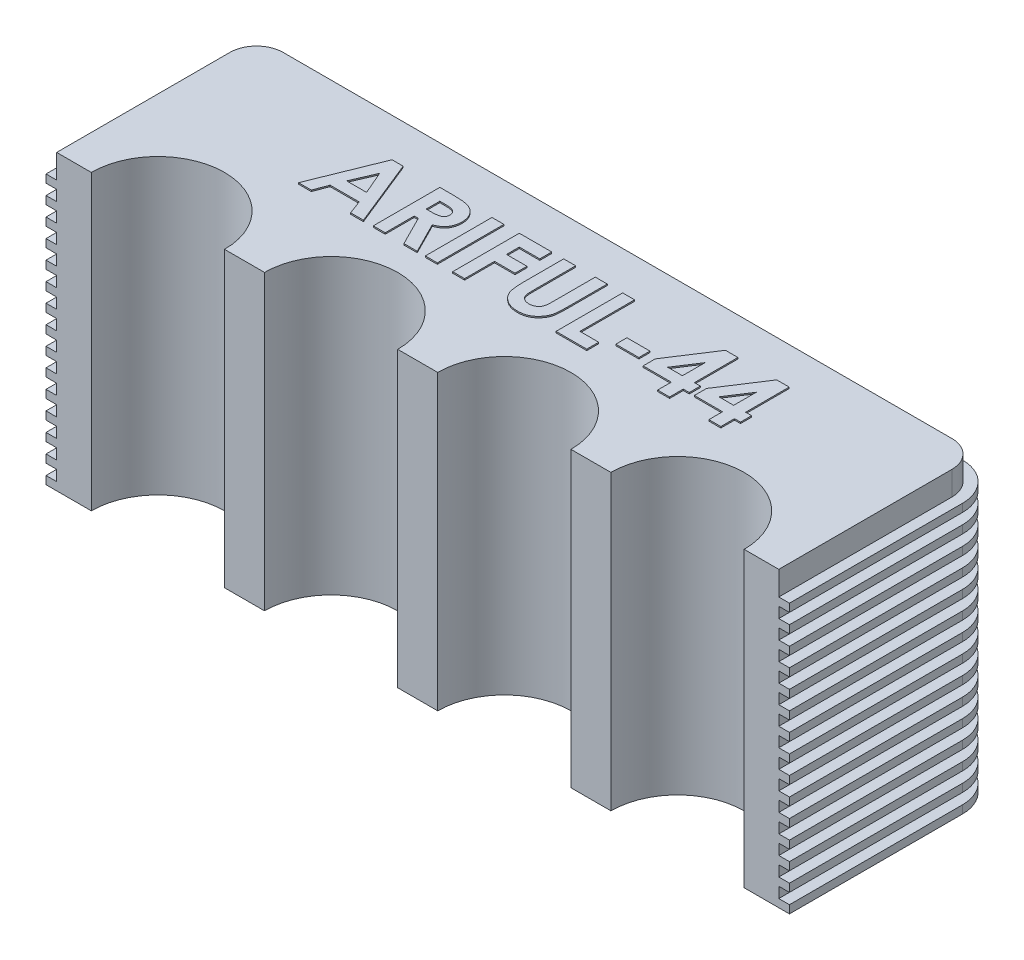
SolidWorks part; units mm, degrees
ref_plane "Front Plane" through (0, 0, 0) normal (0, 0, 1) x (1, 0, 0)
ref_plane "Top Plane" through (0, 0, 0) normal (0, 1, 0) x (1, 0, 0)
ref_plane "Right Plane" through (0, 0, 0) normal (1, 0, 0) x (0, 0, -1)
sketch "Sketch1" plane through (0, 0, 0) normal (0, 1, 0) x (1, 0, 0)
  line L0 (122.5, -37.5) -> (135.5, -37.5)
  line L1 (-135.5, -37.5) -> (-122.5, -37.5)
  line L2 (-135.5, -37.5) -> (-135.5, 27.5)
  line L3 (-125.5, 37.5) -> (125.5, 37.5)
  line L4 (135.5, -37.5) -> (135.5, 27.5)
  line L5 (-135.5, -37.5) -> (135.5, 37.5) construction
  line L6 (-135.5, 37.5) -> (135.5, -37.5) construction
  line L7 (0, 37.5) -> (0, -37.5) construction
  line L8 (57.5, -37.5) -> (72.5, -37.5)
  line L9 (-72.5, -37.5) -> (-57.5, -37.5)
  line L10 (-7.5, -37.5) -> (7.5, -37.5)
  arc A0 (125.5, 37.5) -> (135.5, 27.5) centre (125.5, 27.5) cw
  arc A1 (-135.5, 27.5) -> (-125.5, 37.5) centre (-125.5, 27.5) cw
  arc A2 (122.5, -37.5) -> (72.5, -37.5) centre (97.5, -37.5) ccw
  arc A3 (57.5, -37.5) -> (7.5, -37.5) centre (32.5, -37.5) ccw
  arc A4 (-122.5, -37.5) -> (-72.5, -37.5) centre (-97.5, -37.5) cw
  arc A5 (-57.5, -37.5) -> (-7.5, -37.5) centre (-32.5, -37.5) cw
  point P0 (0, 0)
  dimension "D1" = 10
  dimension "D4" = 25
  dimension "D6" = 50
  dimension "D2" = 271
  dimension "D3" = 65
  dimension "D5" = 13
  dimension "D7" = 15
extrude "Boss-Extrude1" add sketch "Sketch1" along normal blind 110
sketch "Sketch4" plane through (0, 0, 0) normal (0, 1, 0) x (1, 0, 0)
  line L8 (-135.5, -37.5) -> (-139.5, -37.5)
  line L9 (135.5, -37.5) -> (139.5, -37.5)
  line L16 (-139.5, 27.5) -> (-139.5, -41.5)
  line L17 (125.5, 41.5) -> (-125.5, 41.5)
  line L18 (139.5, -41.5) -> (139.5, 27.5)
  line L19 (118.1155, -41.5) -> (139.5, -41.5)
  line L20 (53.1155, -41.5) -> (76.8845, -41.5)
  line L21 (-11.8845, -41.5) -> (11.8845, -41.5)
  line L22 (-76.8845, -41.5) -> (-53.1155, -41.5)
  line L23 (-139.5, -41.5) -> (-118.1155, -41.5)
  line L24 (-139.5, 27.5) -> (-139.5, -37.5)
  line L25 (125.5, 41.5) -> (-125.5, 41.5)
  line L26 (139.5, -37.5) -> (139.5, 27.5)
  line L29 (-135.5, 27.5) -> (-135.5, -37.5)
  line L30 (125.5, 37.5) -> (-125.5, 37.5)
  line L31 (135.5, -37.5) -> (135.5, 27.5)
  line L32 (122.5, -37.5) -> (135.5, -37.5)
  line L33 (57.5, -37.5) -> (72.5, -37.5)
  line L34 (-7.5, -37.5) -> (7.5, -37.5)
  line L35 (-72.5, -37.5) -> (-57.5, -37.5)
  line L36 (-135.5, -37.5) -> (-122.5, -37.5)
  line L37 (-135.5, 27.5) -> (-135.5, -37.5)
  line L38 (125.5, 37.5) -> (-125.5, 37.5)
  line L39 (135.5, -37.5) -> (135.5, 27.5)
  line L41 (57.5, -37.5) -> (72.5, -37.5)
  arc A12 (-125.5, 41.5) -> (-139.5, 27.5) centre (-125.5, 27.5) ccw
  arc A13 (139.5, 27.5) -> (125.5, 41.5) centre (125.5, 27.5) ccw
  arc A14 (118.1155, -41.5) -> (76.8845, -41.5) centre (97.5, -37.5) ccw
  arc A15 (53.1155, -41.5) -> (11.8845, -41.5) centre (32.5, -37.5) ccw
  arc A16 (-11.8845, -41.5) -> (-53.1155, -41.5) centre (-32.5, -37.5) ccw
  arc A17 (-76.8845, -41.5) -> (-118.1155, -41.5) centre (-97.5, -37.5) ccw
  arc A18 (-125.5, 41.5) -> (-139.5, 27.5) centre (-125.5, 27.5) ccw
  arc A19 (139.5, 27.5) -> (125.5, 41.5) centre (125.5, 27.5) ccw
  arc A20 (-125.5, 37.5) -> (-135.5, 27.5) centre (-125.5, 27.5) ccw
  arc A21 (135.5, 27.5) -> (125.5, 37.5) centre (125.5, 27.5) ccw
  arc A22 (122.5, -37.5) -> (72.5, -37.5) centre (97.5, -37.5) ccw
  arc A23 (57.5, -37.5) -> (7.5, -37.5) centre (32.5, -37.5) ccw
  arc A24 (-7.5, -37.5) -> (-57.5, -37.5) centre (-32.5, -37.5) ccw
  arc A25 (-72.5, -37.5) -> (-122.5, -37.5) centre (-97.5, -37.5) ccw
  arc A26 (-125.5, 37.5) -> (-135.5, 27.5) centre (-125.5, 27.5) ccw
  arc A27 (135.5, 27.5) -> (125.5, 37.5) centre (125.5, 27.5) ccw
  dimension "D1" = 4
  dimension "D2" = 0
extrude "Boss-Extrude2" add sketch "Sketch4" along normal blind 3 contours A27 L39 L9 L26 A19 L25 A18 L24 L8 L37 A26 L38
pattern_linear "LPattern2" count 15 spacing 7 along (0, 1, 0) of "Boss-Extrude2"
sketch "Sketch5" plane through (0, 110, 0) normal (0, 1, 0) x (1, 0, 0)
  text T0 "ARIFUL-44" font "Century Gothic" height 25
extrude "Boss-Extrude3" add sketch "Sketch5" along normal blind 0.5
